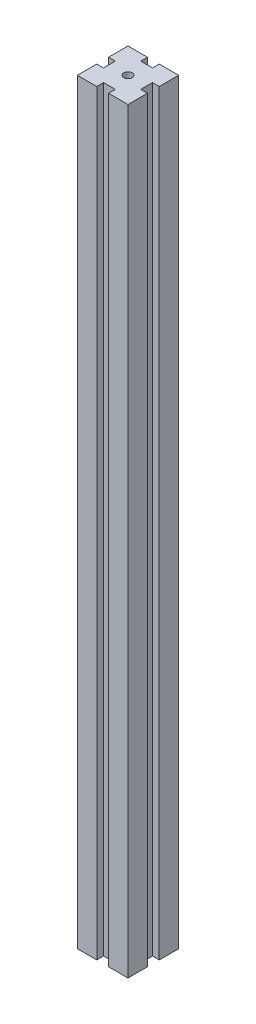
SolidWorks part; units mm, degrees
ref_plane "Front Plane" through (0, 0, 0) normal (0, 0, 1) x (1, 0, 0)
ref_plane "Top Plane" through (0, 0, 0) normal (0, 1, 0) x (1, 0, 0)
ref_plane "Right Plane" through (0, 0, 0) normal (1, 0, 0) x (0, 0, -1)
sketch "Sketch1" plane through (0, 0, 0) normal (0, 1, 0) x (1, 0, 0)
  line L0 (7.5, 15) -> (7.5, 0) construction
  line L1 (0, 0) -> (15, 0)
  line L2 (0, 0) -> (0, 15)
  line L3 (0, 15) -> (15, 15)
  line L4 (15, 0) -> (15, 15)
  line L5 (5.75, 0) -> (9.25, 0)
  line L6 (5.75, 0) -> (5.75, 2)
  line L7 (5.75, 2) -> (9.25, 2)
  line L8 (9.25, 0) -> (9.25, 2)
  line L9 (5.75, 15) -> (9.25, 15)
  line L10 (5.75, 15) -> (5.75, 13)
  line L11 (5.75, 13) -> (9.25, 13)
  line L12 (9.25, 15) -> (9.25, 13)
  line L13 (15, 9.25) -> (13, 9.25)
  line L14 (15, 9.25) -> (15, 5.75)
  line L15 (15, 5.75) -> (13, 5.75)
  line L16 (13, 9.25) -> (13, 5.75)
  line L17 (0, 9.25) -> (2, 9.25)
  line L18 (0, 9.25) -> (0, 5.75)
  line L19 (0, 5.75) -> (2, 5.75)
  line L20 (2, 9.25) -> (2, 5.75)
  line L21 (0, 7.5) -> (15, 7.5) construction
  dimension "D1" = 15
  dimension "D2" = 2
  dimension "15" = 15
  dimension "D3" = 2
  dimension "D4" = 3.5
  dimension "D5" = 3.5
extrude "Boss-Extrude1" add sketch "Sketch1" along normal blind 224 contours L17 L20 L19 L2 L1 L6 L7 L8 L4 L15 L16 L13 L3 L12 L11 L10
sketch "Sketch2" plane through (0, 224, 0) normal (0, 1, 0) x (1, 0, 0)
  line L0 (0, 15) -> (15, 0) construction
  circle A0 centre (7.5, 7.5) radius 1.25
  dimension "D1" = 2.5
extrude "Cut-Extrude1" cut sketch "Sketch2" against normal through all
